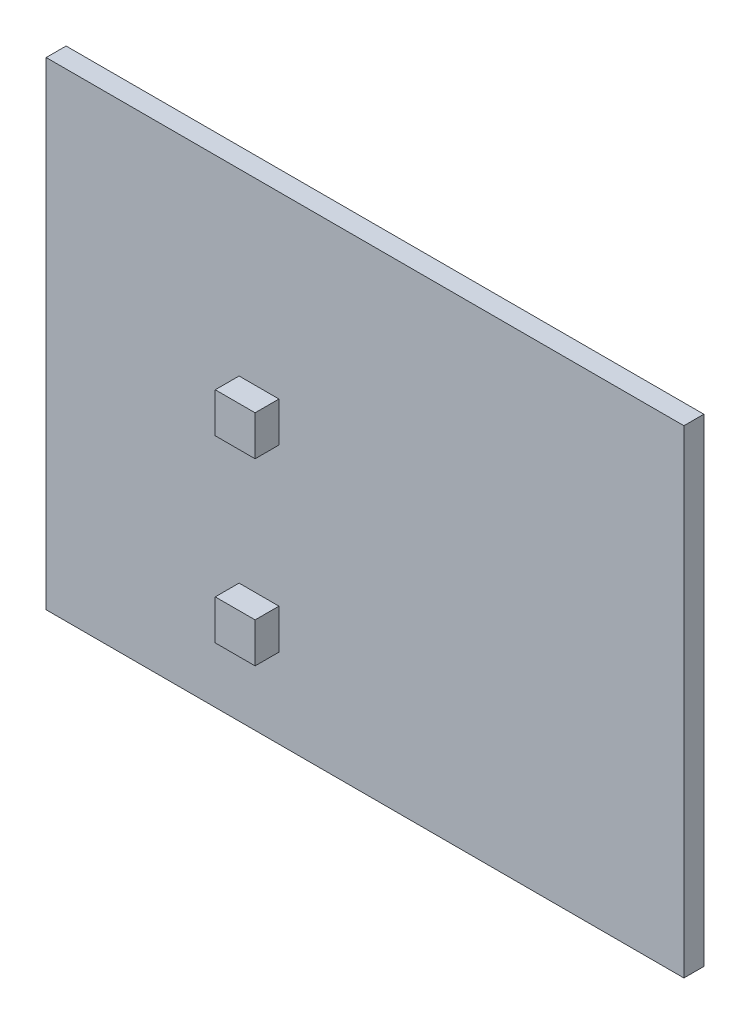
SolidWorks part; units mm, degrees
ref_plane "Front Plane" through (0, 0, 0) normal (0, 0, 1) x (1, 0, 0)
ref_plane "Top Plane" through (0, 0, 0) normal (0, 1, 0) x (1, 0, 0)
ref_plane "Right Plane" through (0, 0, 0) normal (1, 0, 0) x (0, 0, -1)
sketch "Sketch1" plane through (0, 0, 0) normal (0, 0, 1) x (1, 0, 0)
  line L1 (-40, 30) -> (40, 30)
  line L2 (-40, 30) -> (-40, -30)
  line L3 (-40, -30) -> (40, -30)
  line L4 (40, 30) -> (40, -30)
  line L5 (-40, 30) -> (40, -30) construction
  line L6 (-40, -30) -> (40, 30) construction
  point P0 (0, 0)
  dimension "D1" = 80
  dimension "D2" = 60
extrude "Boss-Extrude1" add sketch "Sketch1" along normal blind 2.5
sketch "Sketch2" plane through (0, 0, 2.5) normal (0, 0, 1) x (1, 0, 0)
  line L0 (-13.3, 41.2163) -> (-13.3, -45.5509) construction
  line L1 (40, -30) -> (40, 30) construction
  line L2 (-15.8, -20) -> (-10.8, -20)
  line L3 (-15.8, -20) -> (-15.8, -15)
  line L4 (-15.8, -15) -> (-10.8, -15)
  line L5 (-10.8, -20) -> (-10.8, -15)
  line L6 (-15.8, -20) -> (-10.8, -15) construction
  line L7 (-15.8, -15) -> (-10.8, -20) construction
  line L8 (-15.8, 2.5) -> (-10.8, 2.5)
  line L9 (-15.8, 2.5) -> (-15.8, 7.5)
  line L10 (-15.8, 7.5) -> (-10.8, 7.5)
  line L11 (-10.8, 2.5) -> (-10.8, 7.5)
  line L12 (-15.8, 2.5) -> (-10.8, 7.5) construction
  line L13 (-15.8, 7.5) -> (-10.8, 2.5) construction
  line L14 (40, 30) -> (-40, 30) construction
  point P3 (-13.3, -17.5)
  point P8 (-13.3, 5)
  dimension "D1" = 5
  dimension "D2" = 5
  dimension "D3" = 5
  dimension "D4" = 5
  dimension "D5" = 25
  dimension "D6" = 47.5
  dimension "D7" = 53.3
extrude "Boss-Extrude2" add sketch "Sketch2" along normal blind 2.99
equation "\"D1@Boss-Extrude2\"=7.39-4mm-0.4mm"
